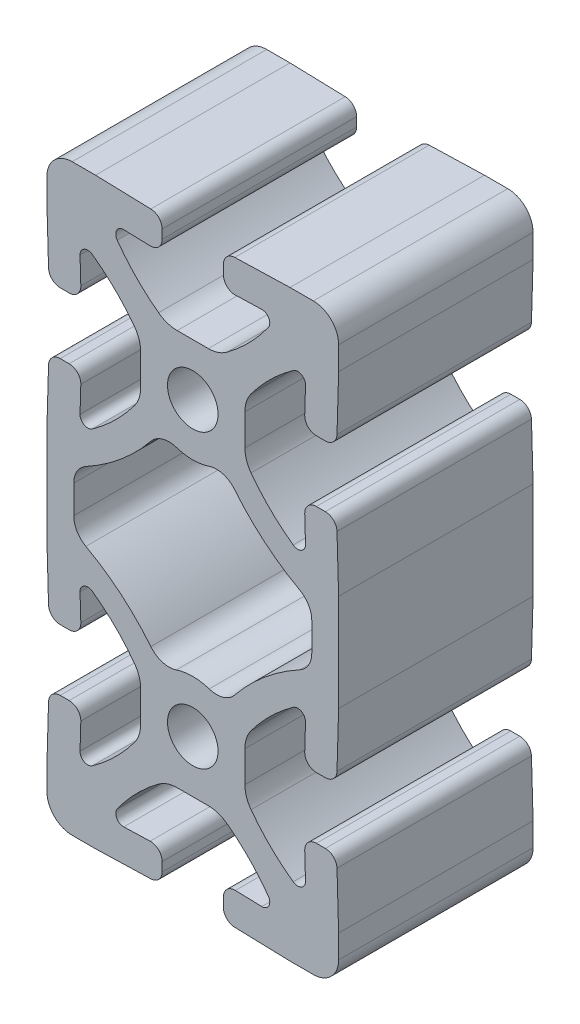
SolidWorks part; units mm, degrees
material "6061 Alloy"
ref_plane "Front" through (0, 0, 0) normal (0, 0, 1) x (1, 0, 0)
ref_plane "Top" through (0, 0, 0) normal (0, 1, 0) x (1, 0, 0)
ref_plane "Right" through (0, 0, 0) normal (1, 0, 0) x (0, 0, -1)
sketch "Sketch1" plane through (0, 0, 0) normal (0, 0, 1) x (1, 0, 0)
  line L0 (-19.05, 12.7) -> (-18.8392, 5.48)
  line L1 (-19.05, -12.7) -> (-18.8392, -5.48)
  line L2 (-19.05, -16.002) -> (-19.05, -12.7)
  line L3 (-19.05, 12.7) -> (-19.05, 16.002)
  line L4 (-19.05, 16.002) -> (-19.05, 22.098)
  line L5 (-14.7241, 9.0129) -> (-14.6236, 5.569)
  line L6 (19.05, 12.7) -> (18.8392, 5.48)
  line L7 (14.7241, 9.0129) -> (14.6236, 5.569)
  line L8 (12.7, -19.05) -> (5.48, -18.8392)
  line L9 (-12.7, -19.05) -> (-5.48, -18.8392)
  line L10 (-15.748, -19.05) -> (-12.7, -19.05)
  line L11 (-4.0005, -17.3158) -> (-4.0005, -16.1469)
  line L12 (-9.0129, -14.7241) -> (-5.569, -14.6236)
  line L13 (4.0005, -17.3158) -> (4.0005, -16.1469)
  line L14 (9.0129, -14.7241) -> (5.569, -14.6236)
  line L15 (-14.7241, -9.0129) -> (-14.6236, -5.569)
  line L16 (-17.3158, -4.0005) -> (-16.1469, -4.0005)
  line L17 (-17.3158, 4.0005) -> (-16.1469, 4.0005)
  line L18 (-6.8072, -2.0409) -> (-6.8072, 2.0409)
  line L19 (-6.8072, 36.0591) -> (-6.8072, 38.1)
  line L20 (-2.0409, -6.8072) -> (2.0409, -6.8072)
  line L21 (6.8072, -2.0409) -> (6.8072, 2.0409)
  line L22 (6.8072, 36.0591) -> (6.8072, 38.1)
  line L23 (19.05, -16.002) -> (19.05, -12.7)
  line L24 (19.05, -12.7) -> (18.8392, -5.48)
  line L25 (15.748, -19.05) -> (12.7, -19.05)
  line L26 (19.05, 12.7) -> (19.05, 16.0321)
  line L27 (19.05, 16.0321) -> (19.05, 22.0679)
  line L28 (17.3158, -4.0005) -> (16.1469, -4.0005)
  line L29 (14.7241, -9.0129) -> (14.6236, -5.569)
  line L30 (17.3158, 4.0005) -> (16.1469, 4.0005)
  line L31 (19.05, 22.0679) -> (19.05, 25.4)
  line L33 (17.3158, 34.0995) -> (16.1469, 34.0995)
  line L34 (14.7241, 47.1129) -> (14.6236, 43.669)
  line L35 (17.3158, 42.1005) -> (16.1469, 42.1005)
  line L36 (-17.3158, 34.0995) -> (-16.1469, 34.0995)
  line L37 (19.05, 50.8) -> (19.05, 53.848)
  line L38 (15.748, 57.15) -> (12.7, 57.15)
  line L39 (19.05, 50.8) -> (18.8392, 43.58)
  line L40 (-17.3158, 42.1005) -> (-16.1469, 42.1005)
  line L41 (6.8072, 40.1409) -> (6.8072, 38.1)
  line L42 (-2.0409, 44.9072) -> (2.0409, 44.9072)
  line L43 (-19.05, 22.098) -> (-19.05, 25.4)
  line L44 (-17.3158, 42.1005) -> (-16.1469, 42.1005)
  line L45 (-6.8072, 40.1409) -> (-6.8072, 38.1)
  line L46 (-15.748, 57.15) -> (-12.7, 57.15)
  line L48 (-14.7241, 47.1129) -> (-14.6236, 43.669)
  line L49 (9.0129, 52.8241) -> (5.569, 52.7236)
  line L50 (4.0005, 55.4158) -> (4.0005, 54.2469)
  line L51 (-9.0129, 52.8241) -> (-5.569, 52.7236)
  line L52 (-4.0005, 55.4158) -> (-4.0005, 54.2469)
  line L53 (-19.05, 50.8) -> (-19.05, 54.102)
  line L54 (-12.7, 57.15) -> (-5.48, 56.9392)
  line L55 (12.7, 57.15) -> (5.48, 56.9392)
  line L56 (14.7241, 29.0871) -> (14.6236, 32.531)
  line L57 (19.05, 25.4) -> (18.8392, 32.62)
  line L58 (-14.7241, 29.0871) -> (-14.6236, 32.531)
  line L61 (-19.05, 53.848) -> (-19.05, 50.8)
  line L62 (-19.05, 50.8) -> (-18.8392, 43.58)
  line L63 (-19.05, 25.4) -> (-18.8392, 32.62)
  line L66 (-15.5448, 20.8952) -> (-15.5448, 17.2048)
  line L67 (15.5448, 20.8952) -> (15.5448, 17.2048)
  arc A0 (-18.8392, 5.48) -> (-17.3158, 4.0005) centre (-17.3158, 5.5245) ccw
  arc A1 (-17.3158, -4.0005) -> (-18.8392, -5.48) centre (-17.3158, -5.5245) ccw
  arc A2 (-19.05, -15.748) -> (-15.748, -19.05) centre (-15.748, -15.748) ccw
  arc A3 (-7.6118, 4.4684) -> (-13.1175, 9.8689) centre (-27.657, -10.4605) ccw
  arc A4 (-5.4799, 7.438) -> (-2.1468, 6.4598) centre (-3.108, 9.3523) ccw
  arc A5 (13.1175, 9.8689) -> (7.6118, 4.4684) centre (27.657, -10.4605) ccw
  arc A6 (2.1468, 6.4598) -> (5.4799, 7.438) centre (3.108, 9.3523) ccw
  arc A7 (9.0129, -14.7241) -> (9.8689, -13.1175) centre (9.0425, -13.7086) ccw
  arc A8 (9.8689, -13.1175) -> (4.4684, -7.6118) centre (-10.4605, -27.657) ccw
  arc A9 (7.6118, -4.4684) -> (13.1175, -9.8689) centre (27.657, 10.4605) ccw
  arc A10 (-4.4684, -7.6118) -> (-9.8689, -13.1175) centre (10.4605, -27.657) ccw
  arc A11 (-5.48, -18.8392) -> (-4.0005, -17.3158) centre (-5.5245, -17.3158) ccw
  arc A12 (-9.8689, -13.1175) -> (-9.0129, -14.7241) centre (-9.0425, -13.7086) ccw
  arc A13 (-4.0005, -16.1469) -> (-5.569, -14.6236) centre (-5.5245, -16.1469) ccw
  arc A14 (4.0005, -17.3158) -> (5.48, -18.8392) centre (5.5245, -17.3158) ccw
  arc A15 (5.569, -14.6236) -> (4.0005, -16.1469) centre (5.5245, -16.1469) ccw
  arc A16 (-2.0409, -6.8072) -> (-4.4684, -7.6118) centre (-2.0409, -10.8712) ccw
  arc A17 (-7.6118, -4.4684) -> (-6.8072, -2.0409) centre (-10.8712, -2.0409) ccw
  arc A18 (-13.1175, -9.8689) -> (-7.6118, -4.4684) centre (-27.657, 10.4605) ccw
  arc A19 (-14.7241, -9.0129) -> (-13.1175, -9.8689) centre (-13.7086, -9.0425) ccw
  arc A20 (-14.6236, -5.569) -> (-16.1469, -4.0005) centre (-16.1469, -5.5245) ccw
  arc A21 (-16.1469, 4.0005) -> (-14.6236, 5.569) centre (-16.1469, 5.5245) ccw
  arc A22 (-6.8072, 2.0409) -> (-7.6118, 4.4684) centre (-10.8712, 2.0409) ccw
  arc A23 (6.8072, -2.0409) -> (7.6118, -4.4684) centre (10.8712, -2.0409) ccw
  arc A24 (4.4684, -7.6118) -> (2.0409, -6.8072) centre (2.0409, -10.8712) ccw
  arc A25 (2.1468, 6.4598) -> (-2.1468, 6.4598) centre (0, 0) ccw
  arc A26 (7.6118, 4.4684) -> (6.8072, 2.0409) centre (10.8712, 2.0409) ccw
  arc A27 (15.748, -19.05) -> (19.05, -15.748) centre (15.748, -15.748) ccw
  arc A28 (13.1175, -9.8689) -> (14.7241, -9.0129) centre (13.7086, -9.0425) ccw
  arc A29 (16.1469, -4.0005) -> (14.6236, -5.569) centre (16.1469, -5.5245) ccw
  arc A30 (18.8392, -5.48) -> (17.3158, -4.0005) centre (17.3158, -5.5245) ccw
  arc A31 (14.6236, 5.569) -> (16.1469, 4.0005) centre (16.1469, 5.5245) ccw
  arc A32 (17.3158, 4.0005) -> (18.8392, 5.48) centre (17.3158, 5.5245) ccw
  arc A33 (13.9616, 14.5318) -> (5.4799, 7.438) centre (27.657, -10.4605) ccw
  arc A34 (-15.5448, 17.2048) -> (-13.9616, 14.5318) centre (-12.4968, 17.2048) ccw
  arc A35 (-5.4799, 7.438) -> (-13.9616, 14.5318) centre (-27.657, -10.4605) ccw
  arc A36 (-13.1175, 9.8689) -> (-14.7241, 9.0129) centre (-13.7086, 9.0425) ccw
  arc A37 (13.9616, 14.5318) -> (15.5448, 17.2048) centre (12.4968, 17.2048) ccw
  arc A38 (14.7241, 9.0129) -> (13.1175, 9.8689) centre (13.7086, 9.0425) ccw
  arc A39 (13.1175, 28.2311) -> (14.7241, 29.0871) centre (13.7086, 29.0575) ccw
  arc A40 (15.5448, 20.8952) -> (13.9616, 23.5682) centre (12.4968, 20.8952) ccw
  arc A41 (-14.7241, 29.0871) -> (-13.1175, 28.2311) centre (-13.7086, 29.0575) ccw
  arc A42 (-13.9616, 23.5682) -> (-5.4799, 30.662) centre (-27.657, 48.5605) ccw
  arc A43 (-13.9616, 23.5682) -> (-15.5448, 20.8952) centre (-12.4968, 20.8952) ccw
  arc A44 (5.4799, 30.662) -> (13.9616, 23.5682) centre (27.657, 48.5605) ccw
  arc A45 (18.8392, 32.62) -> (17.3158, 34.0995) centre (17.3158, 32.5755) ccw
  arc A46 (16.1469, 34.0995) -> (14.6236, 32.531) centre (16.1469, 32.5755) ccw
  arc A47 (17.3158, 42.1005) -> (18.8392, 43.58) centre (17.3158, 43.6245) ccw
  arc A48 (14.6236, 43.669) -> (16.1469, 42.1005) centre (16.1469, 43.6245) ccw
  arc A49 (14.7241, 47.1129) -> (13.1175, 47.9689) centre (13.7086, 47.1425) ccw
  arc A50 (19.05, 53.848) -> (15.748, 57.15) centre (15.748, 53.848) ccw
  arc A51 (6.8072, 36.0591) -> (7.6118, 33.6316) centre (10.8712, 36.0591) ccw
  arc A52 (-2.1468, 31.6402) -> (2.1468, 31.6402) centre (0, 38.1) ccw
  arc A53 (2.0409, 44.9072) -> (4.4684, 45.7118) centre (2.0409, 48.9712) ccw
  arc A54 (7.6118, 42.5684) -> (6.8072, 40.1409) centre (10.8712, 40.1409) ccw
  arc A55 (-7.6118, 33.6316) -> (-6.8072, 36.0591) centre (-10.8712, 36.0591) ccw
  arc A56 (-14.6236, 32.531) -> (-16.1469, 34.0995) centre (-16.1469, 32.5755) ccw
  arc A57 (-16.1469, 42.1005) -> (-14.6236, 43.669) centre (-16.1469, 43.6245) ccw
  arc A58 (-13.1175, 47.9689) -> (-14.7241, 47.1129) centre (-13.7086, 47.1425) ccw
  arc A59 (-7.6118, 42.5684) -> (-13.1175, 47.9689) centre (-27.657, 27.6395) ccw
  arc A60 (-6.8072, 40.1409) -> (-7.6118, 42.5684) centre (-10.8712, 40.1409) ccw
  arc A61 (-4.4684, 45.7118) -> (-2.0409, 44.9072) centre (-2.0409, 48.9712) ccw
  arc A62 (4.0005, 54.2469) -> (5.569, 52.7236) centre (5.5245, 54.2469) ccw
  arc A63 (5.48, 56.9392) -> (4.0005, 55.4158) centre (5.5245, 55.4158) ccw
  arc A64 (-5.569, 52.7236) -> (-4.0005, 54.2469) centre (-5.5245, 54.2469) ccw
  arc A65 (-9.0129, 52.8241) -> (-9.8689, 51.2175) centre (-9.0425, 51.8086) ccw
  arc A66 (-4.0005, 55.4158) -> (-5.48, 56.9392) centre (-5.5245, 55.4158) ccw
  arc A67 (-9.8689, 51.2175) -> (-4.4684, 45.7118) centre (10.4605, 65.757) ccw
  arc A68 (13.1175, 47.9689) -> (7.6118, 42.5684) centre (27.657, 27.6395) ccw
  arc A69 (4.4684, 45.7118) -> (9.8689, 51.2175) centre (-10.4605, 65.757) ccw
  arc A70 (9.8689, 51.2175) -> (9.0129, 52.8241) centre (9.0425, 51.8086) ccw
  arc A71 (5.4799, 30.662) -> (2.1468, 31.6402) centre (3.108, 28.7477) ccw
  arc A72 (7.6118, 33.6316) -> (13.1175, 28.2311) centre (27.657, 48.5605) ccw
  arc A73 (-2.1468, 31.6402) -> (-5.4799, 30.662) centre (-3.108, 28.7477) ccw
  arc A74 (-13.1175, 28.2311) -> (-7.6118, 33.6316) centre (-27.657, 48.5605) ccw
  arc A75 (-15.748, 57.15) -> (-19.05, 53.848) centre (-15.748, 53.848) ccw
  arc A76 (-18.8392, 43.58) -> (-17.3158, 42.1005) centre (-17.3158, 43.6245) ccw
  arc A77 (-17.3158, 34.0995) -> (-18.8392, 32.62) centre (-17.3158, 32.5755) ccw
  circle A78 centre (0, 38.1) radius 3.302
  circle A79 centre (0, 0) radius 3.302
extrude "Extrude1" add sketch "Sketch1" along normal blind 25.4
